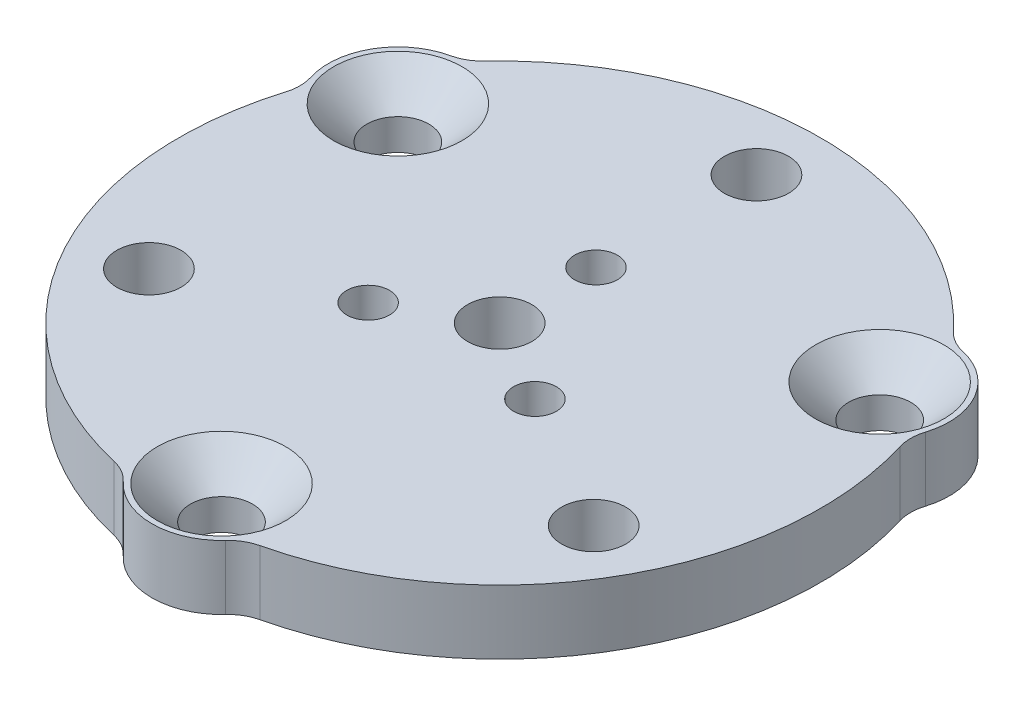
SolidWorks part; units mm, degrees
material "6061 合金"
ref_plane "前视基准面" through (0, 0, 0) normal (0, 0, 1) x (1, 0, 0)
ref_plane "上视基准面" through (0, 0, 0) normal (0, 1, 0) x (1, 0, 0)
ref_plane "右视基准面" through (0, 0, 0) normal (1, 0, 0) x (0, 0, -1)
sketch "草图1" plane through (0, 0, 0) normal (0, 1, 0) x (1, 0, 0)
  line L0 (0, 0) -> (0, -22.4696) construction
  line L1 (0, 0) -> (23.0522, 0) construction
  circle A0 centre (0, 0) radius 13 construction
  circle A1 centre (0, 0) radius 12 construction
  circle A2 centre (0, -13) radius 1.45
  circle A3 centre (-11.2583, 6.5) radius 1.45
  circle A4 centre (11.2583, 6.5) radius 1.45
  circle A5 centre (0, 12) radius 1.5
  circle A6 centre (10.3923, -6) radius 1.5
  circle A7 centre (-10.3923, -6) radius 1.5
  circle A9 centre (0, 0) radius 15
  circle A10 centre (0, 0) radius 4.5 construction
  circle A11 centre (0, 4.5) radius 1
  circle A12 centre (3.8971, -2.25) radius 1
  circle A13 centre (-3.8971, -2.25) radius 1
  circle A14 centre (0, 0) radius 1.5
  point P16 (0, 0)
  point P23 (0, 0)
  point P32 (0, 0)
  dimension "D1" = 26
  dimension "D2" = 24
  dimension "D3" = 2.9
  dimension "D5" = 3
  dimension "D7" = 9
  dimension "D8" = 30
  dimension "D9" = 2
  dimension "D4" = 3
  dimension "D6" = 3
  dimension "D10" = 3
extrude "凸台-拉伸1" add sketch "草图1" along normal blind 3
chamfer "倒角1" distance 1 angle 45 3 edges at (3.8971, 0, 3.25) (-3.8971, 0, 3.25) (0, 0, -3.5)
sketch "草图2" plane through (0, 3, 0) normal (0, 1, 0) x (1, 0, 0)
  circle A0 centre (11.2583, 6.5) radius 3.25
  circle A1 centre (0, -13) radius 3.25
  circle A2 centre (-11.2583, 6.5) radius 3.25
  circle A3 centre (-11.2583, 6.5) radius 1.45
  circle A4 centre (0, -13) radius 1.45
  circle A5 centre (11.2583, 6.5) radius 1.45
  dimension "D1" = 6.5
extrude "凸台-拉伸2" add sketch "草图2" against normal up to surface (3 mm away) up to face at (3.8971, 0, 4.25)
chamfer "倒角2" distance 1.55 angle 45 3 edges at (-11.2583, 3, -5.05) (0, 3, 14.45) (11.2583, 3, -5.05)
fillet "圆角1" radius 2 6 edges at (14.1419, 1.5, -5.0008) (11.4017, 1.5, -9.7468) (-2.7401, 1.5, 14.7476) (2.7401, 1.5, 14.7476) (-11.4017, 1.5, -9.7468) (-14.1419, 1.5, -5.0008)
